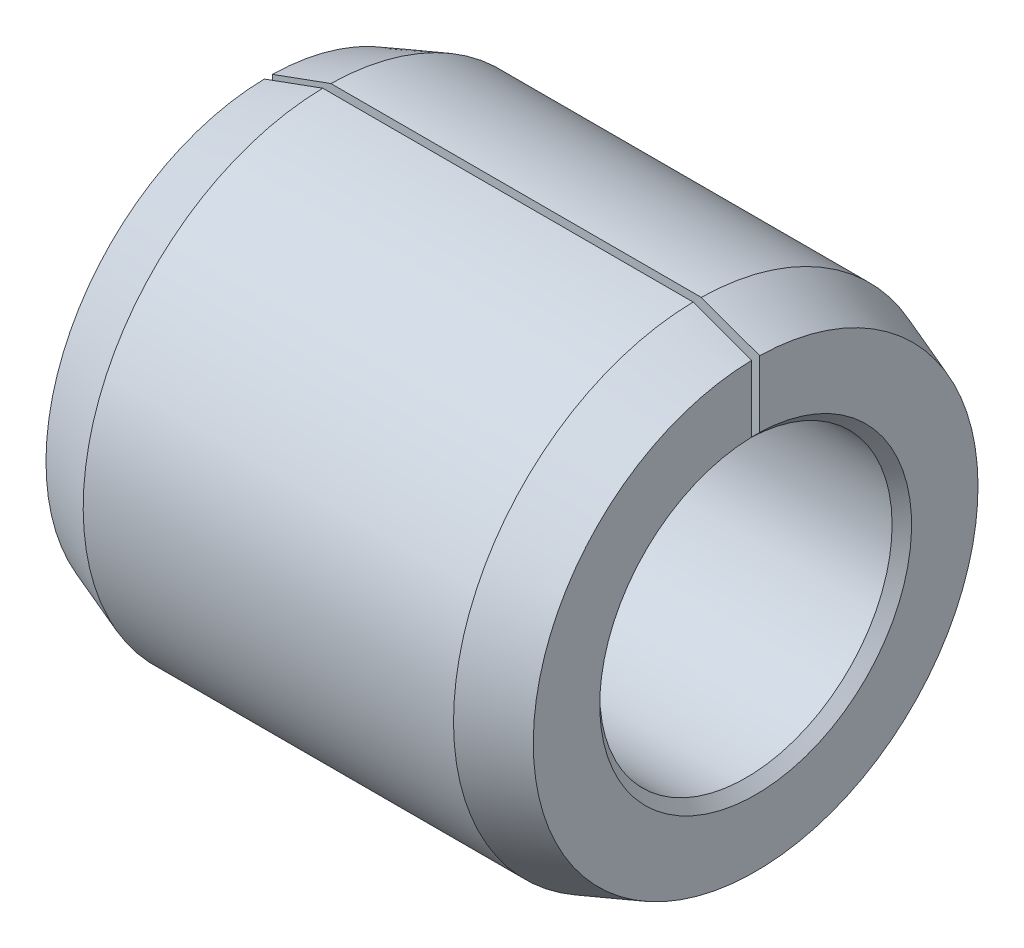
SolidWorks part; units mm, degrees
ref_plane "前视基准面" through (0, 0, 0) normal (0, 0, 1) x (1, 0, 0)
ref_plane "上视基准面" through (0, 0, 0) normal (0, 1, 0) x (1, 0, 0)
ref_plane "右视基准面" through (0, 0, 0) normal (1, 0, 0) x (0, 0, -1)
sketch "草图1" plane through (0, 0, 0) normal (0, 0, 1) x (1, 0, 0)
  line L0 (0, 0) -> (0, 2.2816) construction
  line L1 (0, 0) -> (4.8498, 0) construction
  line L2 (0.6, 2.5) -> (4.4, 2.5)
  line L3 (5, 2.2816) -> (5, 1.6)
  line L4 (4.9, 1.5) -> (0.1, 1.5)
  line L5 (0, 1.6) -> (0, 2.2816)
  line L6 (4.4, 2.5) -> (5, 2.2816)
  line L7 (5, 1.6) -> (4.9, 1.5)
  line L8 (0.1, 1.5) -> (0, 1.6)
  line L9 (0, 2.2816) -> (0.6, 2.5)
  point P6 (5, 1.5)
  point P7 (0, 1.5)
  dimension "D1" = 20
  dimension "Di" = 3
  dimension "D0" = 5
  dimension "B" = 5
  dimension "D2" = 20
  dimension "C0" = 0.6
  dimension "Ci" = 0.1
  dimension "D3" = 45
  dimension "D4" = 45
revolve "旋转1" add sketch "草图1" angle 360 about L1
sketch "草图2" plane through (0, 0, 0) normal (1, 0, 0) x (0, 0, -1)
  line L0 (0, 0) -> (0, 2.5) construction
  line L1 (-0.0417, 0) -> (0.0417, 0)
  line L2 (0.0417, 0) -> (0.0417, 2.5)
  line L3 (-0.0417, 0) -> (-0.0417, 2.5)
  line L4 (-0.0417, 2.5) -> (0.0417, 2.5)
  dimension "D1" = 0.0833
extrude "切除-拉伸1" cut sketch "草图2" along normal through all
